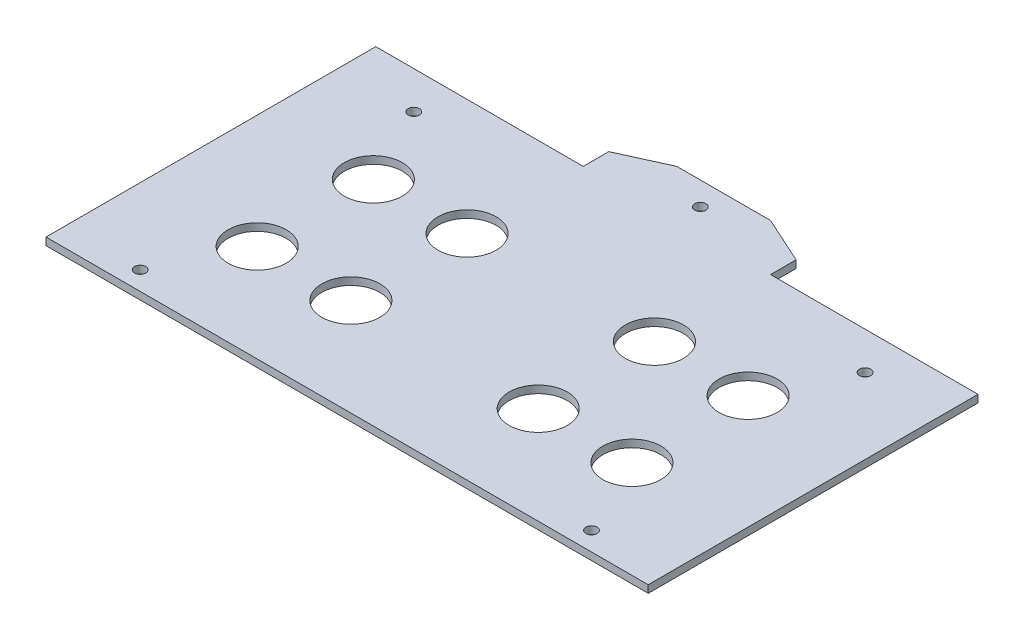
SolidWorks part; units mm, degrees
ref_plane "Front Plane" through (0, 0, 0) normal (0, 0, 1) x (1, 0, 0)
ref_plane "Top Plane" through (0, 0, 0) normal (0, 1, 0) x (1, 0, 0)
ref_plane "Right Plane" through (0, 0, 0) normal (1, 0, 0) x (0, 0, -1)
sketch "Sketch1" plane through (0, 0, 0) normal (0, 1, 0) x (1, 0, 0)
  line L0 (-60.5421, -44) -> (-57.5421, -44)
  line L1 (79.0231, -44) -> (79.0231, -34)
  line L2 (79.0231, -34) -> (-76.6797, -34)
  line L3 (-76.6797, -34) -> (-76.6797, -44)
  line L4 (-76.6797, 24) -> (79.0231, 24)
  line L5 (79.0231, 24) -> (79.0231, 44)
  line L6 (62.8855, 44) -> (59.8855, 44)
  line L7 (-76.6797, 44) -> (-76.6797, 24)
  line L8 (-76.6797, 44) -> (-76.6797, -44)
  line L9 (-60.5421, 44) -> (-57.5421, 44)
  line L10 (-60.5421, -44) -> (-57.5421, -44)
  line L11 (79.0231, 44) -> (79.0231, -44)
  line L12 (-76.6797, 34) -> (79.0231, 34) construction
  line L13 (62.8855, 44) -> (59.8855, 44)
  line L14 (59.8855, -44) -> (62.8855, -44)
  line L15 (-60.5421, -44) -> (-57.5421, -44)
  line L16 (-57.5421, 44) -> (-60.5421, 44)
  line L17 (-76.6797, -39) -> (79.0231, -39) construction
  line L18 (-57.5421, 44) -> (-60.5421, 44)
  line L19 (59.8855, 44) -> (62.8855, 44)
  line L20 (59.8855, -44) -> (62.8855, -44)
  line L21 (59.8855, -44) -> (62.8855, -44)
  line L22 (-59.0421, 44) -> (-59.0421, 24) construction
  line L23 (61.3855, 44) -> (61.3855, 24) construction
  line L24 (61.3855, -44) -> (61.3855, -34) construction
  line L25 (-59.0421, -44) -> (-59.0421, -34) construction
  line L26 (-76.6797, 24) -> (79.0231, 24)
  line L27 (79.0231, 24) -> (79.0231, 44)
  line L28 (79.0231, 44) -> (-76.6797, 44)
  line L29 (-76.6797, 44) -> (-76.6797, 24)
  line L30 (-76.6797, -44) -> (79.0231, -44)
  circle A0 centre (-59.0421, -39) radius 1.5
  circle A1 centre (61.3855, -39) radius 1.5
  circle A2 centre (61.3855, 34) radius 1.5
  circle A3 centre (-59.0421, 34) radius 1.5
  dimension "D1" = 3
extrude "Boss-Extrude2" add sketch "Sketch1" along normal blind 2 contours L11 L4 L8 L2 | L5 L28 L6 L9 L7 L4 A3 A2 | L3 L30 L0 L14 L1 L2 A1 A0
sketch "Sketch2" plane through (0, 2, 0) normal (0, 1, 0) x (1, 0, 0)
  line L0 (79.0231, 44) -> (79.0231, -44)
  line L1 (79.0231, 44) -> (84.0231, 44)
  line L2 (79.0231, -44) -> (84.0231, -44)
  line L3 (84.0231, 44) -> (84.0231, -44)
  line L4 (-76.6797, 44) -> (-76.6797, -44)
  line L5 (-76.6797, 44) -> (-81.6797, 44)
  line L6 (-76.6797, -44) -> (-81.6797, -44)
  line L7 (-81.6797, 44) -> (-81.6797, -44)
  dimension "D1" = 5
  dimension "D2" = 5
extrude "Boss-Extrude3" add sketch "Sketch2" against normal up to surface (2 mm away) up to face at (1.1717, 0, 0)
sketch "Sketch3" plane through (0, 2, 0) normal (0, 1, 0) x (1, 0, 0)
  line L0 (-59.0421, 34) -> (-59.0421, -39) construction
  line L1 (-59.0421, -39) -> (61.3855, -39) construction
  line L2 (61.3855, -39) -> (61.3855, 34) construction
  line L3 (61.3855, 34) -> (-59.0421, 34) construction
  circle A1 centre (26.1717, 13) radius 7.75
  circle A2 centre (51.1717, 13) radius 7.75
  circle A3 centre (-23.8283, 13) radius 7.75
  circle A4 centre (-48.8283, 13) radius 7.75
  circle A5 centre (-48.8283, -18) radius 7.75
  circle A6 centre (-23.8283, -18) radius 7.75
  circle A7 centre (51.1717, -18) radius 7.75
  circle A8 centre (26.1717, -18) radius 7.75
  dimension "D4" = 21
extrude "Cut-Extrude1" cut sketch "Sketch3" against normal blind 10
sketch "Sketch4" plane through (0, 2, 0) normal (0, 1, 0) x (1, 0, 0)
  line L0 (84.0231, 44) -> (-81.6797, 44) construction
  line L1 (-23.8283, 44) -> (26.1717, 44)
  line L2 (26.1717, 44) -> (26.1717, 50.8236)
  line L3 (26.1717, 50.8236) -> (13.6717, 56.4949)
  line L4 (13.6717, 56.4949) -> (-11.3283, 56.4949)
  line L5 (-11.3283, 56.4949) -> (-23.8283, 50.8236)
  line L6 (-23.8283, 50.8236) -> (-23.8283, 44)
  line L7 (1.1717, 56.4949) -> (1.1717, 44) construction
  circle A0 centre (1.1717, 50.2475) radius 1.5
  point P0 (1.1717, 44)
  point P1 (1.1717, 44)
  dimension "D1" = 3
extrude "Boss-Extrude4" add sketch "Sketch4" against normal up to surface (2 mm away) up to face at (-23.8283, 0, 25.75)
sketch "Sketch7" plane through (0, 2, 0) normal (0, 1, 0) x (1, 0, 0)
  line L0 (-81.6797, 44) -> (-81.6797, -44)
  line L1 (-81.6797, 44) -> (-79.1797, 44)
  line L2 (-81.6797, -44) -> (-79.1797, -44)
  line L3 (-79.1797, 44) -> (-79.1797, -44)
  line L4 (84.0231, 44) -> (84.0231, -44)
  line L5 (84.0231, 44) -> (81.5231, 44)
  line L6 (84.0231, -44) -> (81.5231, -44)
  line L7 (81.5231, 44) -> (81.5231, -44)
  line L8 (84.0231, -44) -> (84.0231, 44) construction
  line L9 (-81.6797, -44) -> (84.0231, -44) construction
  dimension "D1" = 2.5
  dimension "D2" = 2.5
extrude "Cut-Extrude2" cut sketch "Sketch7" against normal blind 10
